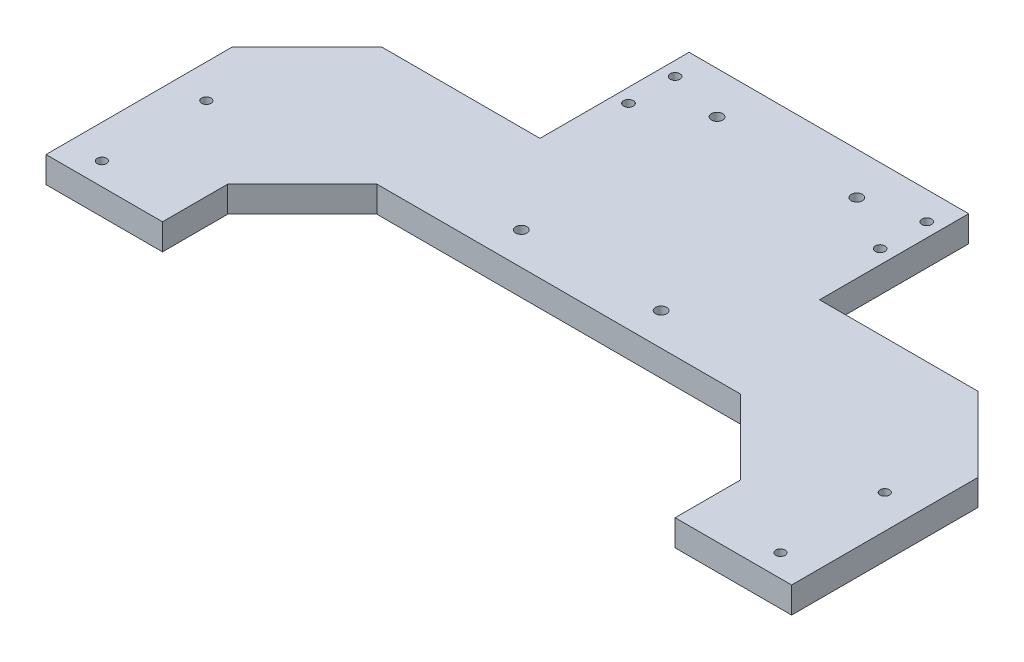
SolidWorks part; units mm, degrees
material "Oak"
ref_plane "Front Plane" through (0, 0, 0) normal (0, 0, 1) x (1, 0, 0)
ref_plane "Top Plane" through (0, 0, 0) normal (0, 1, 0) x (1, 0, 0)
ref_plane "Right Plane" through (0, 0, 0) normal (1, 0, 0) x (0, 0, -1)
sketch "Sketch1" plane through (0, 0, 0) normal (0, 1, 0) x (1, 0, 0)
  line L0 (0, 0) -> (0, -110) construction
  line L2 (-75, -40) -> (-75, 40)
  line L3 (-75, 40) -> (75, 40)
  line L4 (75, -40) -> (75, 40)
  line L5 (-75, -40) -> (75, 40) construction
  line L6 (-75, 40) -> (75, -40) construction
  line L7 (75, -40) -> (200, -40)
  line L8 (-200, -180) -> (200, -180)
  line L9 (-200, -180) -> (-200, -40)
  line L10 (-200, -40) -> (-75, -40)
  line L11 (200, -180) -> (200, -40)
  line L12 (-200, -180) -> (200, -40) construction
  line L13 (-200, -40) -> (200, -180) construction
  point P0 (0, 0)
  point P12 (0, 0)
  dimension "D1" = 150
  dimension "D2" = 80
  dimension "D3" = 400
  dimension "D4" = 140
extrude "Boss-Extrude1" add sketch "Sketch1" along normal blind 14
sketch "Sketch2" plane through (0, 14, 0) normal (0, 1, 0) x (1, 0, 0)
  line L0 (0, 40) -> (0, -180) construction
  line L1 (75, 40) -> (-75, 40) construction
  line L2 (-200, -180) -> (200, -180) construction
  line L3 (-75, 40) -> (-75, -40) construction
  line L4 (-200, -40) -> (-200, -180) construction
  line L10 (137.5, -105) -> (-137.5, -105)
  line L11 (137.5, -105) -> (137.5, -180)
  line L12 (137.5, -180) -> (-137.5, -180)
  line L13 (-137.5, -105) -> (-137.5, -180)
  line L14 (137.5, -105) -> (-137.5, -180) construction
  line L15 (137.5, -180) -> (-137.5, -105) construction
  circle A0 centre (-67.5, 25) radius 2.6
  circle A1 centre (-67.5, 0) radius 2.6
  circle A2 centre (-182, -168) radius 2.5
  circle A3 centre (-182, -112) radius 2.5
  circle A4 centre (-37.5, 17.5) radius 3
  circle A5 centre (-37.5, -87.5) radius 3
  circle A6 centre (37.5, -87.5) radius 3
  circle A7 centre (37.5, 17.5) radius 3
  circle A8 centre (182, -112) radius 2.5
  circle A9 centre (182, -168) radius 2.5
  circle A10 centre (67.5, 0) radius 2.6
  circle A11 centre (67.5, 25) radius 2.6
  point P20 (0, -142.5)
  point P39 (0, -143.6094)
  dimension "D4" = 5.2
  dimension "D5" = 6
  dimension "D6" = 5
  dimension "D9" = 37.5
  dimension "D10" = 56
  dimension "D12" = 18
  dimension "D1" = 105
  dimension "D2" = 22.5
  dimension "D3" = 7.5
  dimension "D7" = 25
  dimension "D8" = 15
  dimension "D11" = 12
  dimension "D13" = 275
  dimension "D14" = 75
extrude "Cut-Extrude1" cut sketch "Sketch2" against normal through all and the other way through all
chamfer "Chamfer1" distance 40 angle 45 4 edges at (200, 7, 40) (-200, 7, 40) (137.5, 7, 105) (-137.5, 7, 105)
